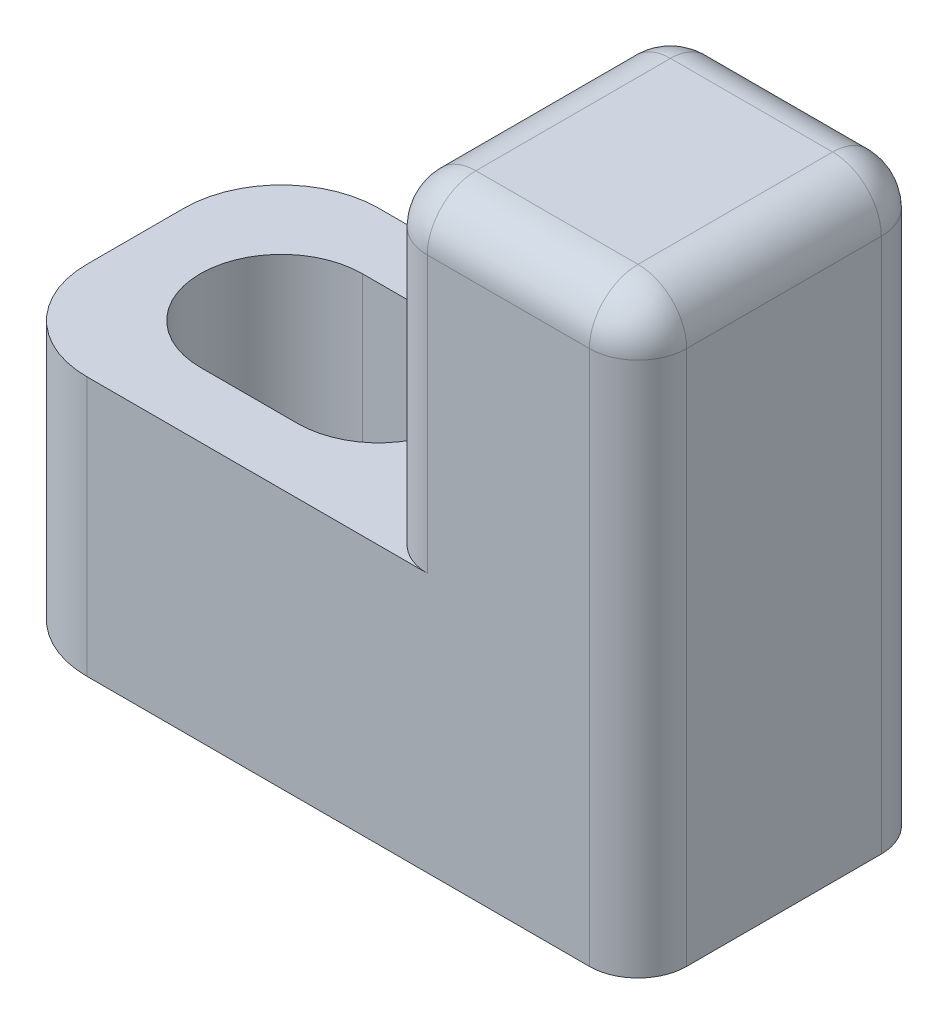
SolidWorks part; units mm, degrees
ref_plane "Front Plane" through (0, 0, 0) normal (0, 0, 1) x (1, 0, 0)
ref_plane "Top Plane" through (0, 0, 0) normal (0, 1, 0) x (1, 0, 0)
ref_plane "Right Plane" through (0, 0, 0) normal (1, 0, 0) x (0, 0, -1)
sketch "Sketch1" plane through (0, 0, 0) normal (0, 1, 0) x (1, 0, 0)
  line L0 (-10, 0) -> (10, 0) construction
  line L1 (-10, 4.5) -> (10, 4.5)
  line L2 (-10, 4.5) -> (-10, -4.5)
  line L3 (-10, -4.5) -> (10, -4.5)
  line L4 (10, 4.5) -> (10, -4.5)
  line L5 (-10, 4.5) -> (10, -4.5) construction
  line L6 (-10, -4.5) -> (10, 4.5) construction
  line L7 (-5.5, 0) -> (-2.5, 0) construction
  line L8 (-5.5, 2.5) -> (-2.5, 2.5)
  line L9 (-5.5, -2.5) -> (-2.5, -2.5)
  arc A1 (-5.5, 2.5) -> (-5.5, -2.5) centre (-5.5, 0) ccw
  arc A2 (-2.5, -2.5) -> (-2.5, 2.5) centre (-2.5, 0) ccw
  point P0 (0, 0)
  point P10 (-4, 0)
  dimension "D3" = 6
  dimension "D5" = 2.5
  dimension "D1" = 9
  dimension "D2" = 20
  dimension "D4" = 3
extrude "Boss-Extrude1" add sketch "Sketch1" along normal blind 8
sketch "Sketch2" plane through (0, 8, 0) normal (0, 1, 0) x (1, 0, 0)
  line L0 (-10, 0) -> (10, 0) construction
  line L1 (-10, 4.5) -> (-10, -4.5) construction
  line L2 (10, -4.5) -> (10, 4.5) construction
  line L3 (-10, -4.5) -> (10, -4.5) construction
  line L8 (10, 4.5) -> (2, 4.5)
  line L9 (10, 4.5) -> (10, -4.5)
  line L10 (10, -4.5) -> (2, -4.5)
  line L11 (2, 4.5) -> (2, -4.5)
  point P13 (2, 0)
  dimension "D1" = 12
extrude "Boss-Extrude2" add sketch "Sketch2" along normal blind 10
fillet "Fillet1" radius 3 2 edges at (-10, 4, -4.5) (-10, 4, 4.5)
fillet "Fillet3" radius 1.5 8 edges at (10, 9, -4.5) (2, 13, -4.5) (10, 9, 4.5) (2, 13, 4.5) (6, 18, 4.5) (10, 18, 0) (6, 18, -4.5) (2, 18, 0)
